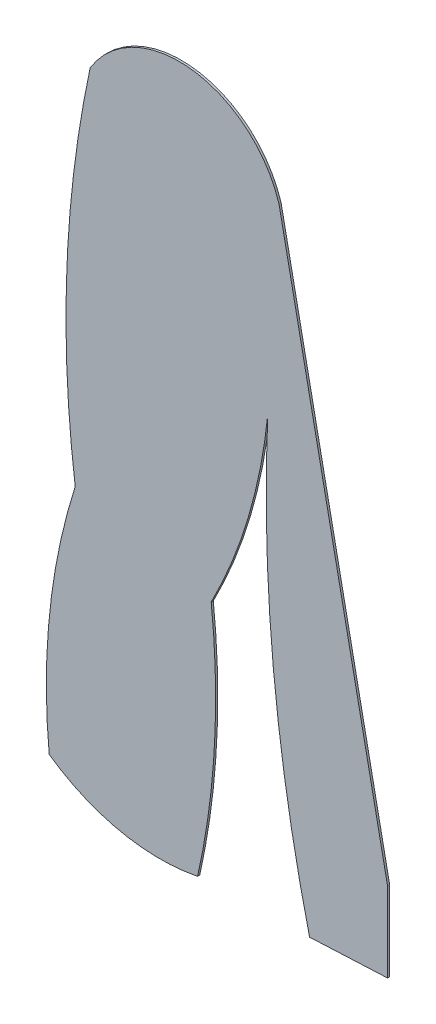
SolidWorks part; units mm, degrees
ref_plane "Alzado" through (0, 0, 0) normal (0, 0, 1) x (1, 0, 0)
ref_plane "Planta" through (0, 0, 0) normal (0, 1, 0) x (1, 0, 0)
ref_plane "Vista lateral" through (0, 0, 0) normal (1, 0, 0) x (0, 0, -1)
sketch "Model" plane through (0, 0, 0) normal (0, 0, 1) x (1, 0, 0)
  line L0 (14.7348, -5.0913) -> (14.7348, -1.3038)
  line L1 (14.7348, -5.0913) -> (11.0371, -5.2632)
  line L2 (9.5861, 24.1332) -> (14.7348, -1.3038)
  arc A0 (-1.3125, -3.9317) -> (5.7266, -5.4208) centre (3.9428, 3.5286) ccw
  arc A1 (5.7266, -5.4208) -> (6.3712, 6.1684) centre (-28.8734, 2.3161) ccw
  arc A2 (6.3712, 6.1684) -> (9.0526, 15.2059) centre (-15.9934, 17.7205) ccw
  arc A3 (9.0526, 15.2059) -> (11.0371, -5.2632) centre (82.0221, 11.9496) ccw
  arc A4 (0.6312, 25.2464) -> (-0.079, 7.6886) centre (51.2581, 14.4052) ccw
  arc A5 (-0.079, 7.6886) -> (-1.3125, -3.9317) centre (27.6029, -1.1253) ccw
  arc A6 (9.5861, 24.1332) -> (0.6312, 25.2464) centre (4.8575, 22.6693) ccw
extrude "Saliente-Extruir1" add sketch "Model" along normal blind 0.1
